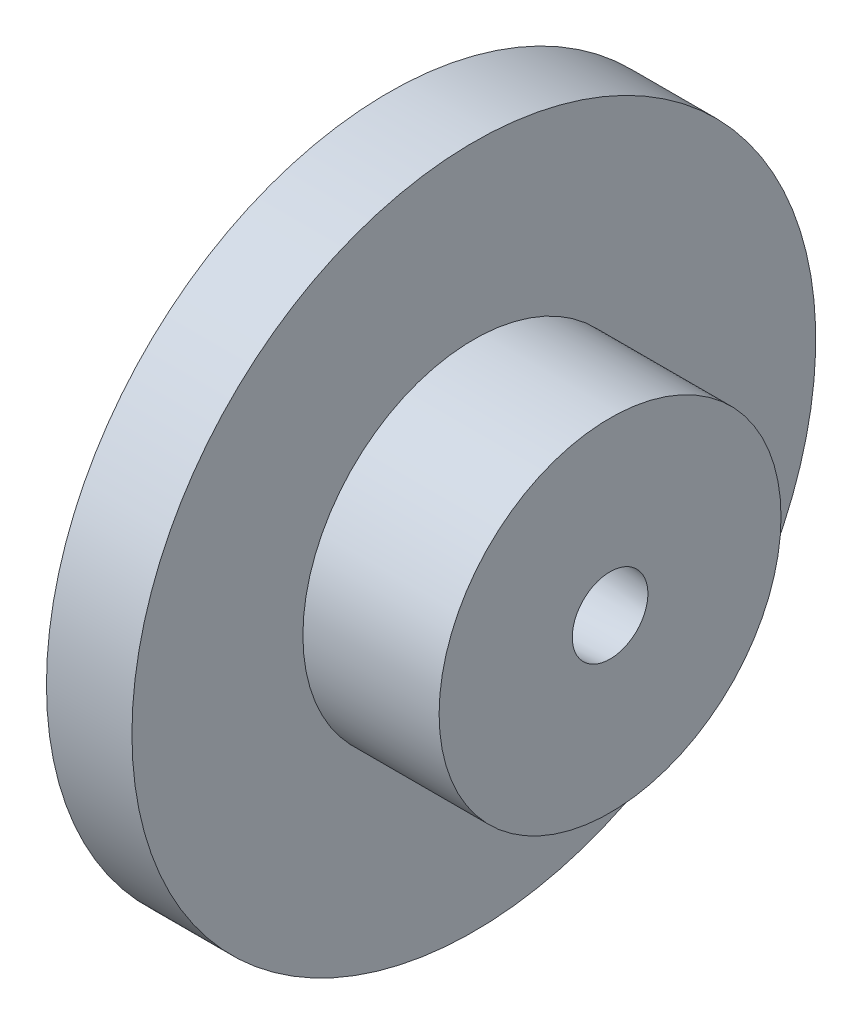
SolidWorks part; units mm, degrees
ref_plane "Front Plane" through (0, 0, 0) normal (0, 0, 1) x (1, 0, 0)
ref_plane "Top Plane" through (0, 0, 0) normal (0, 1, 0) x (1, 0, 0)
ref_plane "Right Plane" through (0, 0, 0) normal (1, 0, 0) x (0, 0, -1)
sketch "Sketch1" plane through (0, 0, 0) normal (0, 0, 1) x (1, 0, 0)
  line L0 (0, 0) -> (50000, 0) construction
  line L1 (0, 0) -> (0, 50000) construction
  line L2 (0, 8.5) -> (0, 50.8)
  line L3 (0, 50.8) -> (12.7, 50.8)
  line L4 (12.7, 50.8) -> (12.7, 25.4)
  line L5 (12.7, 25.4) -> (32.94, 25.4)
  line L6 (32.94, 25.4) -> (32.94, 5.6181)
  line L7 (32.94, 5.6181) -> (0, 8.5)
  dimension "D1" = 50.8
  dimension "D2" = 5
  dimension "D3" = 32.94
  dimension "D4" = 12.7
  dimension "D5" = 8.5
  dimension "D6" = 25.4
revolve "Revolve1" add sketch "Sketch1" angle 360 about L0
ref_plane "Plane1" through (0, 50.8, 0) normal (0, 1, 0) x (1, 0, 0)
equation "\"d_major\"= 17mm"
equation "\"taper_angle\"= 5"
equation "\"d_workhold\"= 2"
equation "\"d_hub\"= 4"
equation "\"length\"= 32.94mm"
equation "\"l_hub\"= 0.5"
equation "\"D1@Sketch1\"=\"d_hub\"/2"
equation "\"D2@Sketch1\"=\"taper_angle\""
equation "\"D3@Sketch1\"=\"length\""
equation "\"D4@Sketch1\"=\"l_hub\""
equation "\"D5@Sketch1\"=\"d_major\"/2"
equation "\"D6@Sketch1\"=\"d_workhold\"/2"
